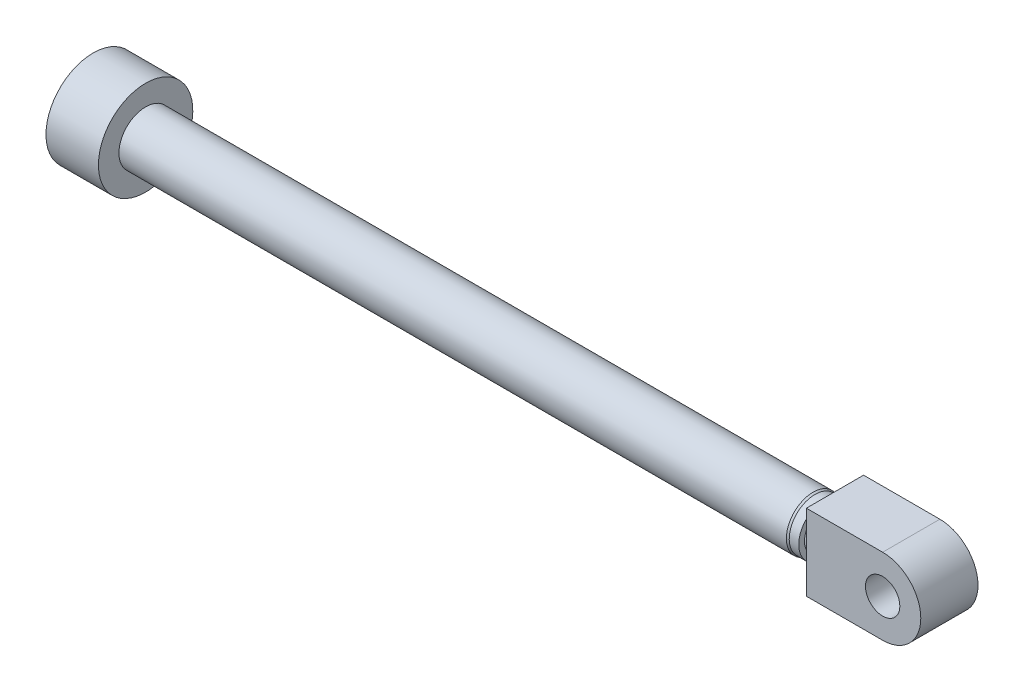
SolidWorks part; units mm, degrees
ref_plane "Plano frontal" through (0, 0, 0) normal (0, 0, 1) x (1, 0, 0)
ref_plane "Plano superior" through (0, 0, 0) normal (0, 1, 0) x (1, 0, 0)
ref_plane "Plano direito" through (0, 0, 0) normal (1, 0, 0) x (0, 0, -1)
sketch "Esboço1" plane through (0, 0, 0) normal (0, 0, 1) x (1, 0, 0)
  line L0 (0, 0) -> (0, 49.5)
  line L1 (0, 49.5) -> (55, 49.5)
  line L2 (55, 49.5) -> (55, 28)
  line L3 (55, 28) -> (755, 28)
  line L4 (755, 28) -> (757, 27)
  line L5 (757, 27) -> (767, 27)
  line L6 (767, 27) -> (767, 21)
  line L7 (767, 21) -> (823, 21)
  line L8 (823, 21) -> (823, 0)
  line L9 (823, 0) -> (0, 0)
  line L10 (823, 0) -> (168.4156, 0) construction
  dimension "D1" = 56
  dimension "D2" = 99
  dimension "D3" = 55
  dimension "D4" = 42
  dimension "D5" = 54
  dimension "D6" = 12
  dimension "D7" = 2
  dimension "D8" = 56
  dimension "D9" = 768
revolve "Revolução1" add sketch "Esboço1" angle 360 about L10
sketch "Esboço2" plane through (823, 0, 0) normal (1, 0, 0) x (0, 0, -1)
  circle A0 centre (0, 0) radius 77.9541
  circle A1 centre (0, 0) radius 21.25
  dimension "D1" = 42.5
extrude "Ressalto-extrusão1" add sketch "Esboço2" against normal blind 45 and the other way blind 75 separate body
sketch "Esboço4" plane through (898, 0, 0) normal (1, 0, 0) x (0, 0, -1)
  circle A0 centre (0, 0) radius 21.25
  dimension "D1" = 42.5
extrude "Ressalto-extrusão3" add sketch "Esboço4" against normal blind 74
sketch "Esboço5" plane through (0, 0, 0) normal (0, 0, 1) x (1, 0, 0)
  line L0 (778, 0) -> (898, 0) construction
  line L1 (778, 77.9541) -> (778, -77.9541) construction
  line L2 (898, -77.9541) -> (898, 77.9541) construction
  line L3 (858, 40) -> (778, 40)
  line L4 (778, 40) -> (778, -40)
  line L5 (858, -40) -> (778, -40)
  line L7 (771.85, -82.8571) -> (904.15, -82.8571)
  line L8 (771.85, -82.8571) -> (771.85, 82.8571)
  line L9 (771.85, 82.8571) -> (904.15, 82.8571)
  line L10 (904.15, -82.8571) -> (904.15, 82.8571)
  line L11 (771.85, -82.8571) -> (904.15, 82.8571) construction
  line L12 (771.85, 82.8571) -> (904.15, -82.8571) construction
  circle A0 centre (858, 0) radius 18
  circle A1 centre (858, 0) radius 40
  point P13 (838, 0)
  dimension "D2" = 36
  dimension "D3" = 80
  dimension "D1" = 80
extrude "Corte-extrusão1" cut sketch "Esboço5" against normal through all both and the other way through all contours L7 L10 L9 L8 A1 L5 L4 L3 | A0
sketch "Esboço6" plane through (0, 40, 0) normal (0, 1, 0) x (1, 0, 0)
  line L0 (858, 66.9092) -> (858, -66.9092) construction
  line L1 (773.5945, -30) -> (942.4055, -30)
  line L2 (773.5945, -30) -> (773.5945, 30)
  line L3 (773.5945, 30) -> (942.4055, 30)
  line L4 (942.4055, -30) -> (942.4055, 30)
  line L5 (773.5945, -30) -> (942.4055, 30) construction
  line L6 (773.5945, 30) -> (942.4055, -30) construction
  line L8 (773.5945, -104.8771) -> (942.4055, -104.8771)
  line L9 (773.5945, -104.8771) -> (773.5945, 104.8771)
  line L10 (773.5945, 104.8771) -> (942.4055, 104.8771)
  line L11 (942.4055, -104.8771) -> (942.4055, 104.8771)
  line L12 (773.5945, -104.8771) -> (942.4055, 104.8771) construction
  line L13 (773.5945, 104.8771) -> (942.4055, -104.8771) construction
  point P0 (858, 0)
  point P7 (858, 0)
  line M6 (858, 66.9092) -> (778, 66.9092)
  line M7 (778, 66.9092) -> (778, -66.9092)
  line M8 (778, -66.9092) -> (858, -66.9092)
  line M9 (858, -66.9092) -> (858, 66.9092)
  dimension "D1" = 60
extrude "Corte-extrusão2" cut sketch "Esboço6" against normal through all both and the other way through all contours L3 L11 L10 L9 M7 M6 M9 | L3 M7 M9 M6 | L8 L11 L1 L9 M9 M8 M7 | L1 M7 M8 M9
sketch "Esboço7" plane through (771.85, 0, 0) normal (1, 0, 0) x (0, 0, -1)
  circle A0 centre (0, 0) radius 21
  dimension "D1" = 42
extrude "Ressalto-extrusão4" add sketch "Esboço7" along normal blind 20
